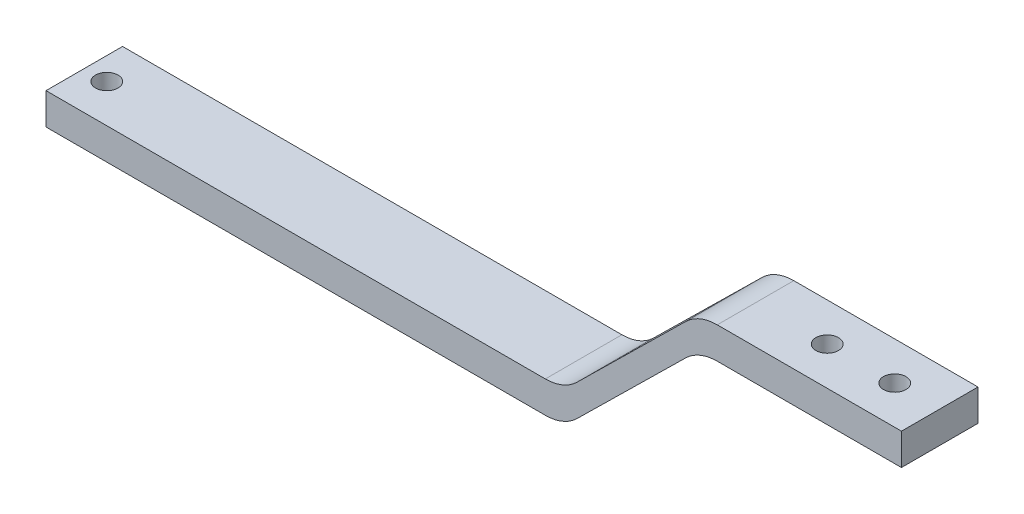
SolidWorks part; units mm, degrees
ref_plane "Front Plane" through (0, 0, 0) normal (0, 0, 1) x (1, 0, 0)
ref_plane "Top Plane" through (0, 0, 0) normal (0, 1, 0) x (1, 0, 0)
ref_plane "Right Plane" through (0, 0, 0) normal (1, 0, 0) x (0, 0, -1)
sketch "Sketch1" plane through (0, 0, 0) normal (0, 0, 1) x (1, 0, 0)
  line L0 (-135.9325, 32.1332) -> (-20.9325, 32.1332)
  line L1 (-20.9325, 32.1332) -> (9.0675, 61.6332)
  line L2 (9.0675, 61.6332) -> (54.0675, 61.6332)
  line L3 (54.0675, 61.6332) -> (54.0675, 54.6332)
  line L4 (54.0675, 54.6332) -> (9.0675, 54.6332)
  line L5 (9.0675, 54.6332) -> (-20.9325, 25.1332)
  line L6 (-20.9325, 25.1332) -> (-135.9325, 25.1332)
  line L7 (-135.9325, 25.1332) -> (-135.9325, 32.1332)
  dimension "D1" = 115
  dimension "D2" = 30
  dimension "D3" = 29.5
  dimension "D4" = 45
  dimension "D5" = 115
  dimension "D6" = 30
  dimension "D7" = 7
  dimension "D8" = 7
extrude "Extrude1" add sketch "Sketch1" along normal blind 17
fillet "Fillet1" radius 10 4 edges at (9.0675, 54.6332, 8.5) (9.0675, 61.6332, 8.5) (-20.9325, 25.1332, 8.5) (-20.9325, 32.1332, 8.5)
sketch "Sketch2" plane through (0, 54.6332, 0) normal (0, -1, 0) x (1, 0, 0)
  line L0 (54.0675, 17) -> (54.0675, 0) construction
  circle A0 centre (44.0675, 8.5) radius 2.5
  circle A1 centre (29.0675, 8.5) radius 2.5
  dimension "D1" = 5
  dimension "D2" = 5
  dimension "D3" = 10
  dimension "D4" = 15
extrude "Extrude2" cut sketch "Sketch2" against normal blind 17
sketch "Sketch3" plane through (0, 25.1332, 0) normal (0, -1, 0) x (1, 0, 0)
  line L0 (-135.9325, 17) -> (-135.9325, 0) construction
  circle A0 centre (-130.9325, 8.5) radius 2.5
  point P2 (-135.9325, 8.5)
  dimension "D1" = 5
  dimension "D2" = 5
extrude "Extrude3" cut sketch "Sketch3" against normal blind 17
